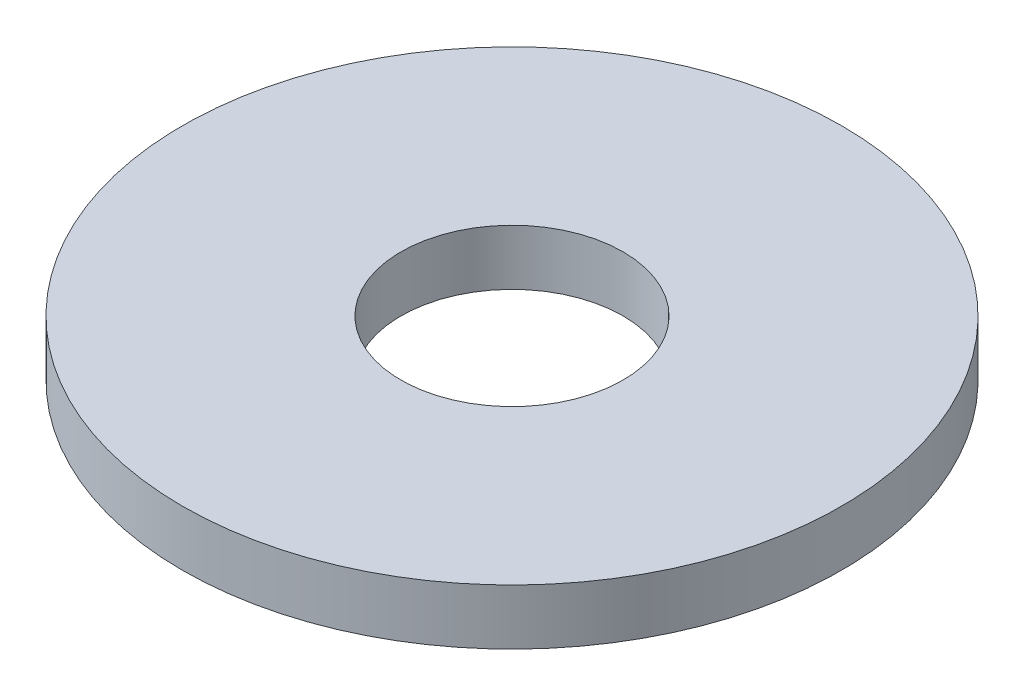
SolidWorks part; units mm, degrees
material "1.4301 (X5CrNi18-10)"
ref_plane "Vorne" through (0, 0, 0) normal (0, 0, 1) x (1, 0, 0)
ref_plane "Oben" through (0, 0, 0) normal (0, 1, 0) x (1, 0, 0)
ref_plane "Rechts" through (0, 0, 0) normal (1, 0, 0) x (0, 0, -1)
sketch "Skizze1" plane through (0, 0, 0) normal (1, 0, 0) x (0, 0, -1)
  line L0 (0, 0) -> (0, 4.7663) construction
  line L1 (-6, 0) -> (-17.8, 0)
  line L2 (-6, 0) -> (-6, 3)
  line L3 (-6, 3) -> (-17.8, 3)
  line L4 (-17.8, 0) -> (-17.8, 3)
  dimension "D1" = 3
  dimension "D2" = 6
  dimension "D3" = 17.8
revolve "Rotation1" add sketch "Skizze1" angle 360 about L0
